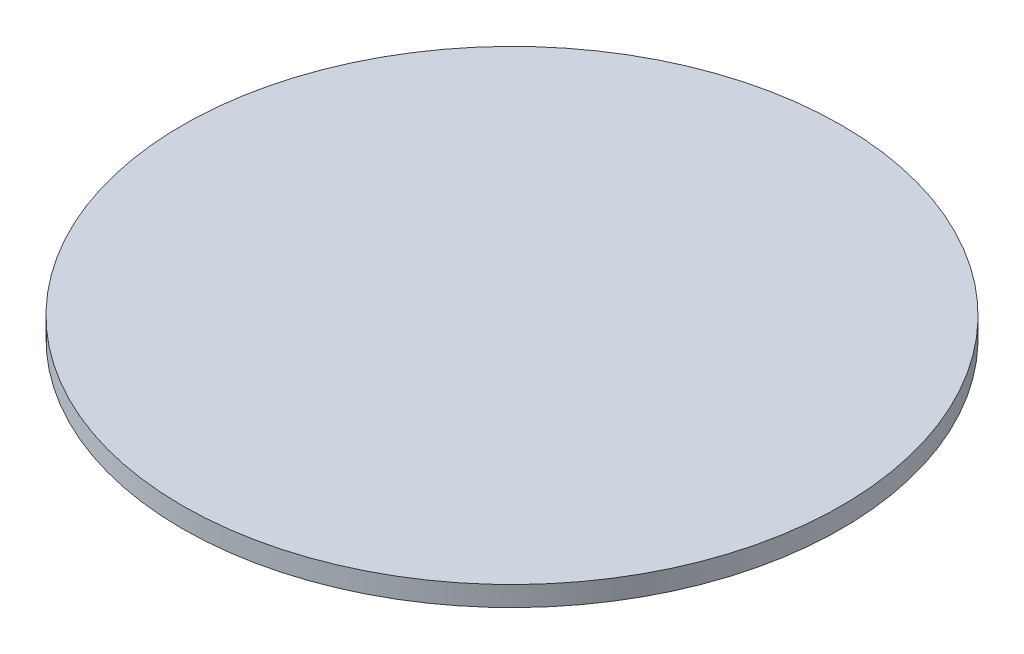
SolidWorks part; units mm, degrees
ref_plane "Спереди" through (0, 0, 0) normal (0, 0, 1) x (1, 0, 0)
ref_plane "Сверху" through (0, 0, 0) normal (0, 1, 0) x (1, 0, 0)
ref_plane "Справа" through (0, 0, 0) normal (1, 0, 0) x (0, 0, -1)
sketch "Эскиз1" plane through (0, 0, 0) normal (0, 0, 1) x (1, 0, 0)
  line L0 (0, 0) -> (0, 2)
  line L1 (0, 2) -> (16.5, 2)
  line L2 (16.5, 2) -> (16.5, 1)
  line L3 (16.5, 1) -> (13.5, 1)
  line L4 (13.5, 1) -> (13.5, 0)
  line L5 (13.5, 0) -> (0, 0)
  dimension "D1" = 2
  dimension "D2" = 16.5
  dimension "D3" = 13.5
  dimension "D4" = 1
revolve "Повернуть1" add sketch "Эскиз1" angle 360 about L0
